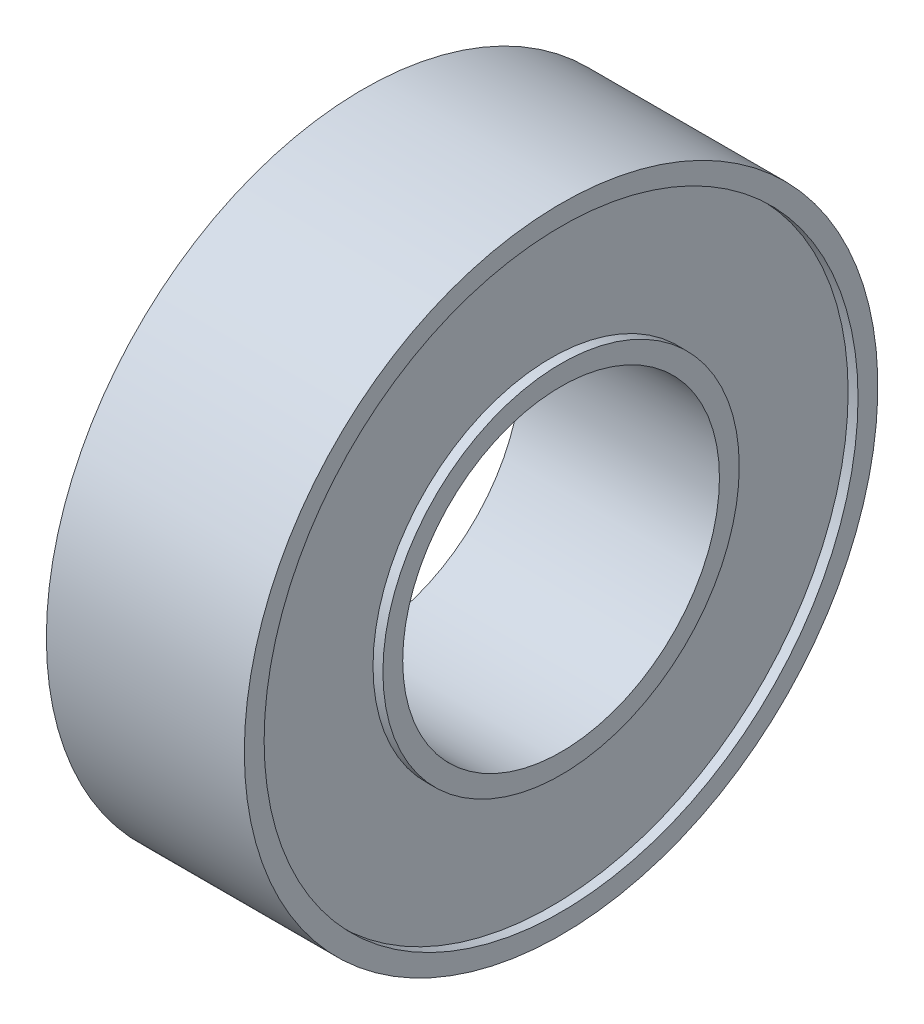
SolidWorks part; units mm, degrees
ref_plane "Front Plane" through (0, 0, 0) normal (0, 0, 1) x (1, 0, 0)
ref_plane "Top Plane" through (0, 0, 0) normal (0, 1, 0) x (1, 0, 0)
ref_plane "Right Plane" through (0, 0, 0) normal (1, 0, 0) x (0, 0, -1)
sketch "Sketch1" plane through (0, 0, 0) normal (0, 0, 1) x (1, 0, 0)
  line L0 (-2.5, 8) -> (2.5, 8)
  line L1 (2.5, 8) -> (2.5, 7.5)
  line L2 (2.5, 7.5) -> (2.25, 7.5)
  line L3 (2.25, 7.5) -> (2.25, 4.5)
  line L4 (2.25, 4.5) -> (2.5, 4.5)
  line L5 (2.5, 4.5) -> (2.5, 4)
  line L6 (2.5, 4) -> (-2.5, 4)
  line L7 (0, 4) -> (0, 8) construction
  line L8 (0, 0) -> (2.8502, 0) construction
  line L9 (-2.5, 4.5) -> (-2.5, 4)
  line L10 (-2.25, 4.5) -> (-2.5, 4.5)
  line L11 (-2.25, 7.5) -> (-2.25, 4.5)
  line L12 (-2.5, 7.5) -> (-2.25, 7.5)
  line L13 (-2.5, 8) -> (-2.5, 7.5)
  dimension "D1" = 8
  dimension "D2" = 16
  dimension "D3" = 5
  dimension "D4" = 0.5
  dimension "D5" = 0.25
revolve "Revolve1" add sketch "Sketch1" angle 360 about L8
